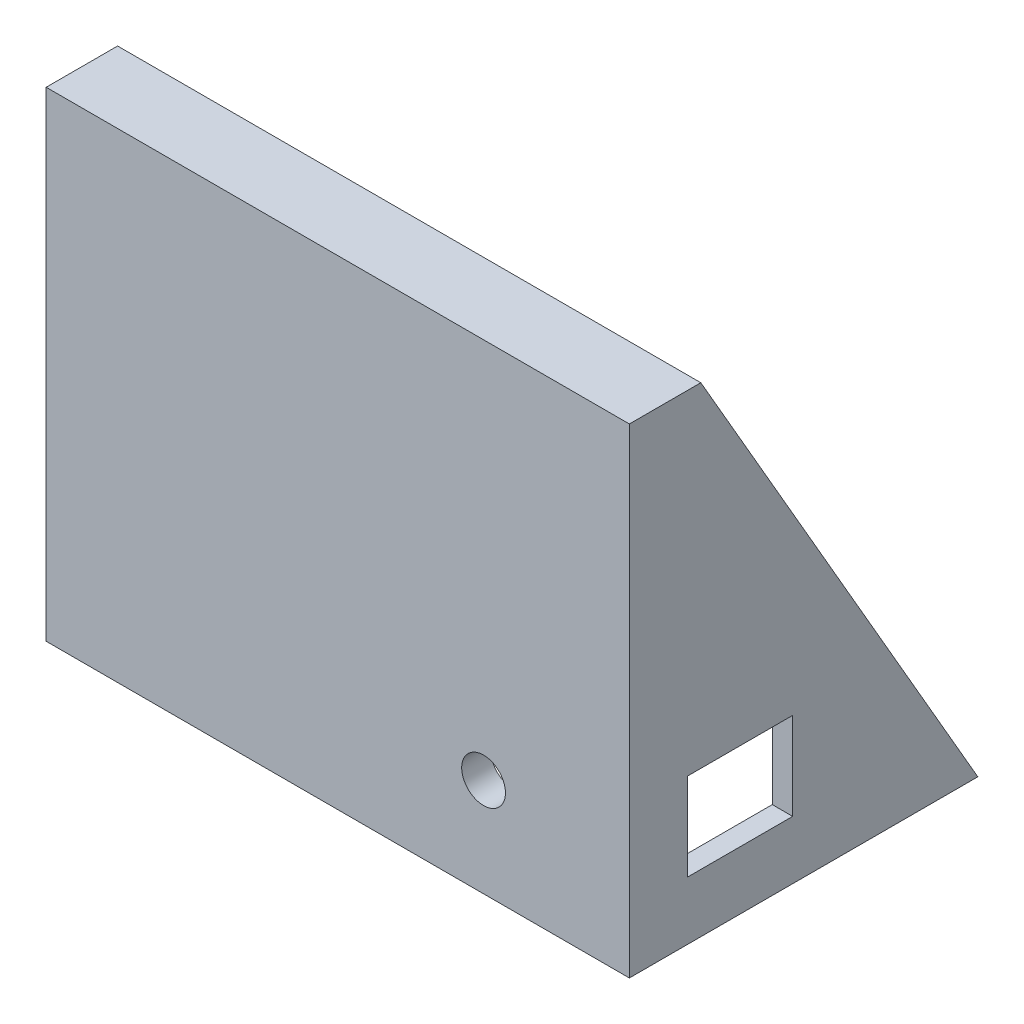
SolidWorks part; units mm, degrees
material "ABS"
ref_plane "Front Plane" through (0, 0, 0) normal (0, 0, 1) x (1, 0, 0)
ref_plane "Top Plane" through (0, 0, 0) normal (0, 1, 0) x (1, 0, 0)
ref_plane "Right Plane" through (0, 0, 0) normal (1, 0, 0) x (0, 0, -1)
sketch "Sketch2" plane through (0, 0, 0) normal (1, 0, 0) x (0, 0, -1)
  line L0 (0, 60.7895) -> (24.5, 60.7895)
  line L1 (24.5, 60.7895) -> (119.5, -103.7554)
  line L2 (119.5, -103.7554) -> (0, -103.7554)
  line L3 (0, -103.7554) -> (0, 60.7895)
  dimension "D1" = 24.5
  dimension "D2" = 190
  dimension "D3" = 120
extrude "Boss-Extrude1" add sketch "Sketch2" along normal blind 200
shell "Shell1" thickness 10
sketch "Sketch4" plane through (0, 25.8062, -44.6976) normal (0, 0.5, -0.866) x (-1, 0, 0)
  line L0 (-200, 40.3952) -> (0, 40.3952) construction
  line L1 (-200, -149.6048) -> (-200, 40.3952) construction
  line L3 (0, -149.6048) -> (0, 40.3952) construction
  line L4 (-200, -149.6048) -> (0, -149.6048) construction
  circle A0 centre (-185, 0.3952) radius 2.5
  circle A1 centre (-185, -109.6048) radius 2.5
  circle A2 centre (-155, -139.6048) radius 2.5
  circle A3 centre (-45, -139.6048) radius 2.5
  circle A4 centre (-15, -109.6048) radius 2.5
  circle A5 centre (-15, 0.3952) radius 2.5
  circle A6 centre (-45, 30.3952) radius 2.5
  circle A7 centre (-155, 30.3952) radius 2.5
  dimension "D1" = 5
  dimension "D2" = 5
  dimension "D3" = 5
  dimension "D4" = 5
  dimension "D5" = 5
  dimension "D6" = 5
  dimension "D7" = 5
  dimension "D8" = 5
  dimension "D10" = 15
  dimension "D11" = 40
  dimension "D12" = 45
  dimension "D13" = 45
  dimension "D14" = 15
  dimension "D15" = 10
  dimension "D16" = 40
  dimension "D17" = 40
  dimension "D18" = 15
  dimension "D19" = 10
  dimension "D20" = 45
  dimension "D21" = 15
  dimension "D22" = 40
  dimension "D23" = 10
  dimension "D24" = 45
  dimension "D9" = 10
extrude "Cut-Extrude2" cut sketch "Sketch4" against normal blind 5
sketch "Sketch5" plane through (200, 0, 0) normal (1, 0, 0) x (0, 0, -1)
  line L0 (0, 60.7895) -> (0, -103.7554) construction
  line L1 (20, -53.7554) -> (56, -53.7554)
  line L2 (20, -53.7554) -> (20, -83.7554)
  line L3 (20, -83.7554) -> (56, -83.7554)
  line L4 (56, -53.7554) -> (56, -83.7554)
  line L5 (0, -103.7554) -> (119.5, -103.7554) construction
  point P6 (20, -68.7554)
  dimension "D1" = 36
  dimension "D2" = 30
  dimension "D3" = 20
  dimension "D4" = 20
extrude "Cut-Extrude3" cut sketch "Sketch5" against normal blind 20
sketch "Sketch6" plane through (0, 0, 0) normal (0, 0, 1) x (1, 0, 0)
  line L0 (200, 60.7895) -> (200, -103.7554) construction
  line L1 (193, -103.7554) -> (7, -103.7554) construction
  circle A0 centre (150, -70.0359) radius 7.5
  dimension "D1" = 15
  dimension "D2" = 50
extrude "Cut-Extrude4" cut sketch "Sketch6" against normal blind 20
sketch "Sketch7" plane through (0, 0, 0) normal (0, 0, 1) x (1, 0, 0)
  line L0 (200, -103.7554) -> (0, -103.7554) construction
  line L1 (0, 60.7895) -> (200, 60.7895)
  line L2 (0, 60.7895) -> (0, -103.7554)
  line L3 (0, -103.7554) -> (200, -103.7554)
  line L4 (200, 60.7895) -> (200, -103.7554)
extrude "Boss-Extrude2" [suppressed] add sketch "Sketch7" along normal blind 60
sketch "Sketch8" plane through (0, 0, -10) normal (0, 0, -1) x (-1, 0, 0)
  circle A0 centre (-150, -70.0359) radius 7.5
extrude "Cut-Extrude5" [suppressed] cut sketch "Sketch8" against normal through all
sketch "Sketch14" plane through (0, 60.7895, 0) normal (0, 1, 0) x (1, 0, 0)
  line L0 (0, -60) -> (-6.1272, -62.0017)
  line L1 (-6.1272, -62.0017) -> (0, -51.8189)
  line L2 (200, -60) -> (206.2634, -60)
  line L3 (206.2634, -60) -> (203.6169, -51.899)
  line L4 (203.6169, -51.899) -> (200, -51.899)
  line L8 (0, -51.8189) -> (0, -60)
  line L9 (0, -60) -> (200, -60)
  line L10 (200, -60) -> (200, -51.899)
  spline S2 degree 3 poles (200, -51.899) (198.8085, -50.8812) (197.5963, -49.8841) (194.763, -47.639) (193.1253, -46.4034) (188.1518, -42.829) (184.7446, -40.6125) (177.7611, -36.4874) (174.1845, -34.5791) (166.8707, -31.0548) (163.134, -29.4377) (157.4116, -27.2257) (155.4927, -26.5272) (151.6403, -25.2084) (149.7056, -24.5876) (143.8764, -22.8379) (139.957, -21.8218) (132.0538, -20.0801) (128.07, -19.3547) (122.0464, -18.483) (120.0305, -18.2286) (115.9827, -17.7924) (113.9494, -17.6105) (107.8336, -17.1755) (103.7701, -17.0354) (91.619, -17.0522) (83.571, -17.6433) (71.578, -19.3991) (67.5936, -20.1303) (61.6376, -21.4536) (59.6557, -21.9326) (55.699, -22.9683) (53.737, -23.5218) (47.9015, -25.2879) (44.0776, -26.6062) (36.5638, -29.5265) (32.8738, -31.1287) (25.6323, -34.6265) (22.0813, -36.5233) (15.1288, -40.6338) (11.7272, -42.8472) (7.5776, -45.8312) (6.7517, -46.4398) (5.1169, -47.6744) (4.3082, -48.3002) (2.3195, -49.8771) (1.15, -50.8385) (0, -51.8189) knots 0.222344 0.222344 0.222344 0.222344 0.234375 0.234375 0.25 0.25 0.28125 0.28125 0.3125 0.3125 0.34375 0.34375 0.359375 0.359375 0.375 0.375 0.40625 0.40625 0.4375 0.4375 0.453125 0.453125 0.46875 0.46875 0.5 0.5 0.5625 0.5625 0.59375 0.59375 0.609375 0.609375 0.625 0.625 0.65625 0.65625 0.6875 0.6875 0.71875 0.71875 0.75 0.75 0.757812 0.757812 0.765625 0.765625 0.777234 0.777234 0.777234 0.777234
  line M17 (0, 24.5) -> (0, 0)
  line M19 (200, 0) -> (200, 24.5)
extrude "Cut-Extrude7" [suppressed] cut sketch "Sketch14" against normal through all contours L3 L4 L2 M19 | L10 S2 L9 M17 | L8 L1 L0
sketch "Sketch16" [suppressed] plane through (0, 60.7895, 0) normal (0, 1, 0) x (1, 0, 0)
  line L0 (200, -51.899) -> (217.6123, -51.899)
  line L1 (217.6123, -51.899) -> (217.6123, -73.519)
  line L2 (217.6123, -73.519) -> (206.6918, -73.519)
  line L3 (-9.5151, -73.519) -> (-9.5151, -51.899)
  line L4 (-9.5151, -51.899) -> (200, -51.899)
  line L5 (206.6918, -73.519) -> (-9.5151, -73.519)
extrude "Cut-Extrude8" [suppressed] cut sketch "Sketch16" against normal through all
